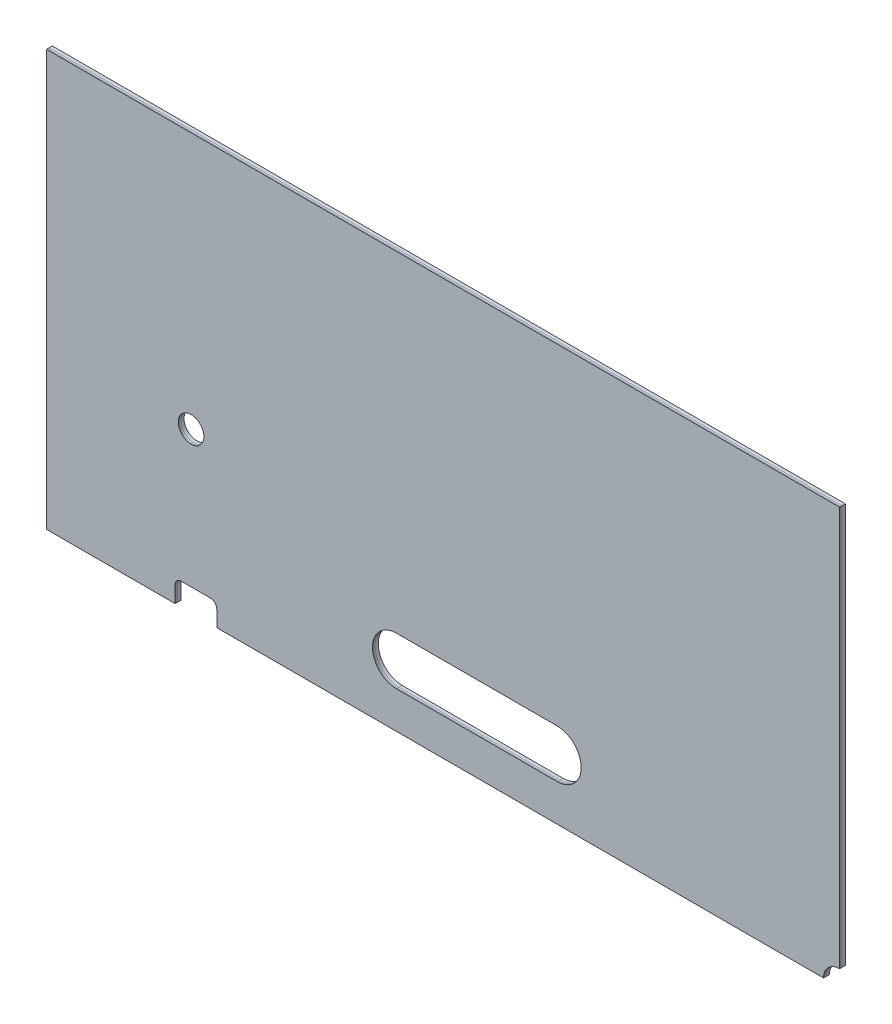
SolidWorks part; units mm, degrees
ref_plane "Płaszczyzna przednia" through (0, 0, 0) normal (0, 0, 1) x (1, 0, 0)
ref_plane "Płaszczyzna górna" through (0, 0, 0) normal (0, 1, 0) x (1, 0, 0)
ref_plane "Płaszczyzna prawa" through (0, 0, 0) normal (1, 0, 0) x (0, 0, -1)
sketch "Szkic1" plane through (0, 0, 0) normal (0, 0, 1) x (1, 0, 0)
  line L0 (0, 0) -> (0, 129.5)
  line L1 (0, 0) -> (-247, 0)
  line L5 (0, 129.5) -> (-247, 129.5)
  line L8 (-247, 129.5) -> (-247, 0)
  point P4 (0, 0)
  dimension "D1" = 247
  dimension "D3" = 129.5
extrude "Dodanie-wyciągnięcie1" add sketch "Szkic1" along normal blind 1
sketch "Szkic2" plane through (0, 0, 1) normal (0, 0, 1) x (1, 0, 0)
  line L10 (0, 0) -> (-247, 0)
  line L15 (0, 129.5) -> (0, 0)
  line L16 (-247, 0) -> (-247, 129.5)
  line L17 (-247, 129.5) -> (0, 129.5)
extrude "Dodanie-wyciągnięcie2" add sketch "Szkic2" along normal blind 0.5 separate body
sketch "Szkic3" plane through (0, 0, 1.5) normal (0, 0, 1) x (1, 0, 0)
  line L16 (0, 129.5) -> (-247, 129.5) construction
  line L17 (0, 0) -> (-247, 0)
  line L18 (0, 0) -> (0, 129.5)
  line L19 (0, 129.5) -> (-247, 129.5)
  line L20 (-247, 0) -> (-247, 129.5)
  line L21 (-247, 129.5) -> (-247, 0) construction
extrude "Dodanie-wyciągnięcie3" add sketch "Szkic3" along normal blind 0.3 separate body
sketch "Szkic5" plane through (0, 0, 1.8) normal (0, 0, 1) x (1, 0, 0)
  line L0 (-138, 19) -> (-88, 19) construction
  line L1 (-138, 26.5) -> (-88, 26.5)
  line L2 (-138, 11.5) -> (-88, 11.5)
  line L3 (-247, 0) -> (0, 0) construction
  line L4 (0, 0) -> (0, 129.5) construction
  arc A2 (-138, 26.5) -> (-138, 11.5) centre (-138, 19) ccw
  arc A3 (-88, 11.5) -> (-88, 26.5) centre (-88, 19) ccw
  point P2 (-113, 19)
  dimension "D1" = 50
  dimension "D2" = 15
  dimension "D3" = 19
  dimension "D4" = 88
extrude "Wytnij-wyciągnięcie2" cut sketch "Szkic5" against normal through all
sketch "Szkic6" plane through (0, 0, 1.8) normal (0, 0, 1) x (1, 0, 0)
  line L0 (0, 0) -> (0, 129.5) construction
  line L1 (-247, 0) -> (0, 0) construction
  line L2 (0, 0) -> (-5, 0)
  line L3 (0, 0) -> (0, 5)
  arc A0 (0, 5) -> (-5, 0) centre (0, 0) ccw
  dimension "D1" = 5
extrude "Wytnij-wyciągnięcie3" cut sketch "Szkic6" against normal through all
sketch "Szkic8" plane through (0, 0, 1.8) normal (0, 0, 1) x (1, 0, 0)
  line L0 (-207, 0) -> (-207, 7)
  line L1 (-247, 0) -> (-5, 0) construction
  line L2 (-207, 7) -> (-194, 7)
  line L3 (-194, 7) -> (-194, 0)
  line L4 (-207, 0) -> (-194, 0)
  dimension "D1" = 13
  dimension "D2" = 7
  dimension "D3" = 40
extrude "Wytnij-wyciągnięcie4" cut sketch "Szkic8" against normal through all
fillet "Zaokrąglenie1" radius 2 2 edges at (-194, 7, 0.5) (-207, 7, 0.5)
fillet "Zaokrąglenie2" radius 2 2 edges at (-207, 7, 1.25) (-194, 7, 1.25)
fillet "Zaokrąglenie3" radius 2 2 edges at (-207, 7, 1.65) (-194, 7, 1.65)
sketch "Szkic9" plane through (0, 0, 1.8) normal (0, 0, 1) x (1, 0, 0)
  line L0 (-247, 129.5) -> (-247, 0) construction
  line L1 (0, 129.5) -> (-247, 129.5) construction
  circle A0 centre (-202, 49.5) radius 4
  point P6 (-198.57, 107.4866)
  dimension "D1" = 8
  dimension "D2" = 45
  dimension "D3" = 80
extrude "Wytnij-wyciągnięcie5" cut sketch "Szkic9" against normal through all
